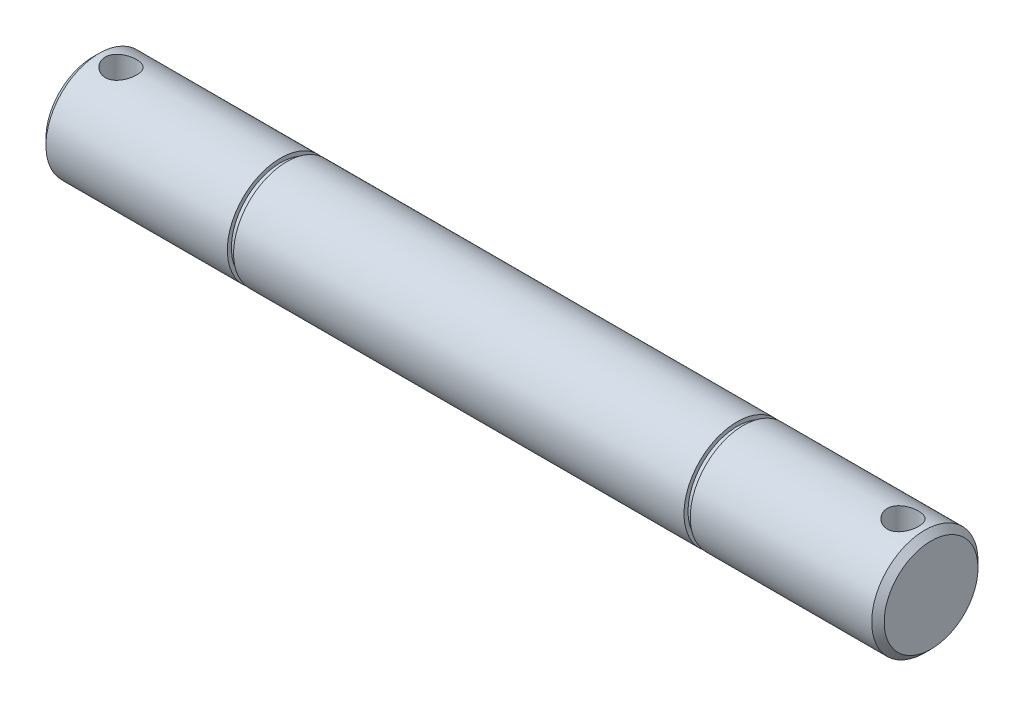
SolidWorks part; units mm, degrees
ref_plane "Front Plane" through (0, 0, 0) normal (0, 0, 1) x (1, 0, 0)
ref_plane "Top Plane" through (0, 0, 0) normal (0, 1, 0) x (1, 0, 0)
ref_plane "Right Plane" through (0, 0, 0) normal (1, 0, 0) x (0, 0, -1)
sketch "Sketch1" plane through (0, 0, 0) normal (1, 0, 0) x (0, 0, -1)
  circle A0 centre (0, 0) radius 8.5
  dimension "D1" = 17
extrude "Boss-Extrude1" add sketch "Sketch1" along normal blind 134
chamfer "Chamfer1" distance 1 angle 45 2 edges at (0, 0, -8.5) (134, 0, -8.5)
sketch "Sketch2" plane through (0, 0, 0) normal (0, 1, 0) x (1, 0, 0)
  line L0 (67, 8.5) -> (67, -8.4168) construction
  line L1 (133, 8.5) -> (1, 8.5) construction
  circle A0 centre (4.5, 0) radius 2.5
  circle A1 centre (129.5, 0) radius 2.5
  dimension "D1" = 5
  dimension "D2" = 4.5
extrude "Cut-Extrude1" cut sketch "Sketch2" against normal through all both and the other way through all
ref_plane "Plane1" through (104, 0, 0) normal (1, 0, 0) x (0, 0, -1)
sketch "Sketch3" plane through (104, 0, 0) normal (1, 0, 0) x (0, 0, -1)
  circle A0 centre (0, 0) radius 7.85
  circle A1 centre (0, 0) radius 8.5
  dimension "D1" = 15.7
  dimension "D2" = 17
extrude "Cut-Extrude2" cut sketch "Sketch3" against normal blind 1
ref_plane "Plane2" through (67, 0, 0) normal (1, 0, 0) x (0, 0, -1)
mirror "Mirror1" about plane through (67, 0, 0) normal (1, 0, 0) of "Cut-Extrude2"
